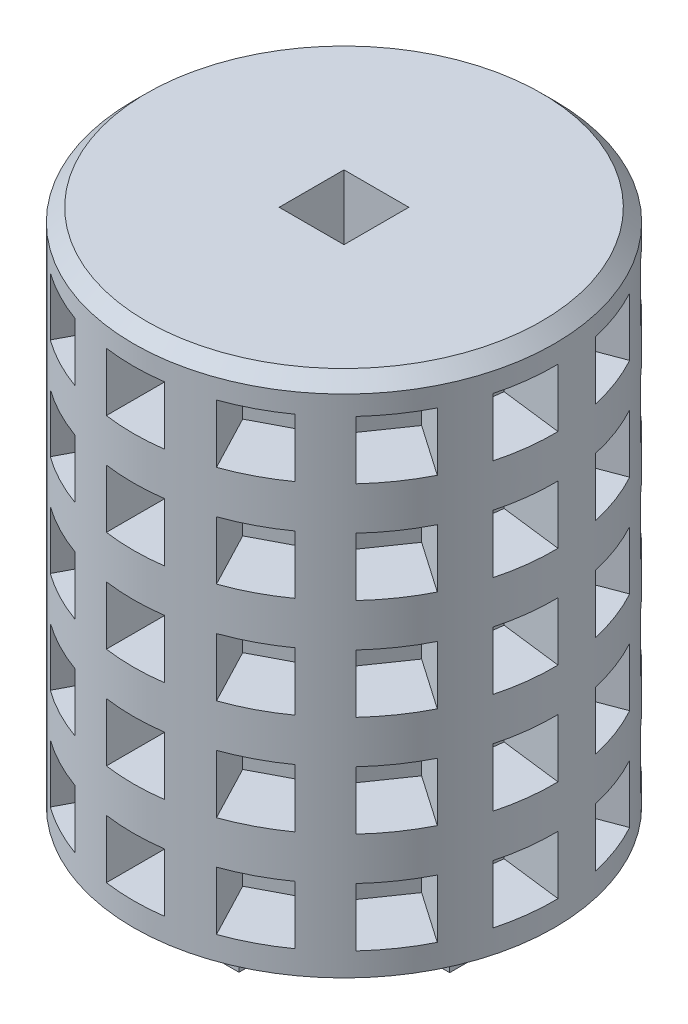
SolidWorks part; units mm, degrees
ref_plane "Front Plane" through (0, 0, 0) normal (0, 0, 1) x (1, 0, 0)
ref_plane "Top Plane" through (0, 0, 0) normal (0, 1, 0) x (1, 0, 0)
ref_plane "Right Plane" through (0, 0, 0) normal (1, 0, 0) x (0, 0, -1)
sketch "Sketch1" plane through (0, 0, 0) normal (0, 1, 0) x (1, 0, 0)
  circle A0 centre (0, 0) radius 41.2369
  dimension "D1" = 82.4738
extrude "Boss-Extrude1" add sketch "Sketch1" along normal blind 203.2 contours A0
sketch "Sketch2" plane through (0, 0, 0) normal (0, -1, 0) x (-1, 0, 0)
  line L3 (0, -6.35) -> (6.35, -6.35)
  line L5 (0, 6.35) -> (6.35, 6.35)
  line L6 (6.35, -6.35) -> (6.35, 6.35)
  line L7 (0, -6.35) -> (-6.35, -6.35)
  line L9 (0, 6.35) -> (-6.35, 6.35)
  line L10 (-6.35, -6.35) -> (-6.35, 6.35)
extrude "Cut-Extrude1" cut sketch "Sketch2" against normal through all contours L10 L9 L5 L6 L3 L7
ref_plane "Plane2" through (0, 0, 60.96) normal (0, 0, 1) x (1, 0, 0)
chamfer "Chamfer1" distance 2.54 angle 45 1 edges at (0, 203.2, 41.2369)
chamfer "Chamfer2" distance 2.54 angle 45 1 edges at (0, 0, 41.2369)
ref_plane "Plane3" through (0, 0, 48.26) normal (0, 0, 1) x (1, 0, 0)
ref_plane "Plane4" through (0, 0, 41.402) normal (0, 0, 1) x (1, 0, 0)
sketch "Sketch3" plane through (0, 0, 41.402) normal (0, 0, 1) x (1, 0, 0)
  line L0 (-41.2369, 200.66) -> (41.2369, 200.66) construction
  line L1 (0, 200.66) -> (-9.525, 200.66)
  line L2 (-9.525, 200.66) -> (9.525, 181.61)
  line L3 (-3.81, 181.61) -> (-9.525, 181.61)
  line L4 (-9.525, 200.66) -> (-9.525, 181.61)
  line L5 (-9.525, 181.61) -> (9.525, 200.66)
  line L6 (0, 200.66) -> (9.525, 200.66)
  line L8 (-3.81, 181.61) -> (9.525, 181.61)
  line L9 (9.525, 200.66) -> (9.525, 181.61)
sketch "Sketch6" plane through (0, 0, 41.402) normal (0, 0, 1) x (1, 0, 0)
  line L0 (-9.525, 181.61) -> (9.525, 200.66) construction
  line L3 (0, 196.85) -> (5.715, 196.85)
  line L4 (5.715, 191.135) -> (5.715, 196.85)
  line L5 (-9.525, 200.66) -> (9.525, 181.61) construction
  line L8 (0, 196.85) -> (-5.715, 196.85)
  line L9 (-5.715, 191.135) -> (-5.715, 196.85)
  line L12 (-5.715, 191.135) -> (-5.715, 185.42)
  line L13 (-5.715, 185.42) -> (5.715, 185.42)
  line L14 (5.715, 191.135) -> (5.715, 185.42)
extrude "Cut-Extrude3" cut sketch "Sketch6" against normal blind 12.7 contours L3 L4 L14 L13 L12 L9 L8
pattern_linear "LPattern1" count 10 spacing 19.812 along (0, -1, 0) of "Cut-Extrude3"
pattern_circular "CirPattern1" count 13 every 27.7 about axis through (0, 0, 0) along (0, 1, 0) of "LPattern1", "Cut-Extrude3"
sketch "Sketch7" plane through (0, 0, 0) normal (0, -1, 0) x (1, 0, 0)
  circle A0 centre (0, 0) radius 41.2369
extrude "Cut-Extrude4" cut sketch "Sketch7" against normal blind 101.6 contours A0
sketch "Sketch9" plane through (0, 101.6, 0) normal (0, -1, 0) x (1, 0, 0)
  line L3 (-6.35, -6.35) -> (-6.35, 6.35) construction
  line L4 (-26.543, -5.969) -> (-24.257, -5.969)
  line L5 (-26.543, -5.969) -> (-26.543, 5.969)
  line L6 (-26.543, 5.969) -> (-24.257, 5.969)
  line L7 (-24.257, -5.969) -> (-24.257, 5.969)
  line L8 (-26.543, -5.969) -> (-24.257, 5.969) construction
  line L9 (-26.543, 5.969) -> (-24.257, -5.969) construction
  line L10 (-5.969, 24.257) -> (5.969, 24.257)
  line L11 (-5.969, 24.257) -> (-5.969, 26.543)
  line L12 (-5.969, 26.543) -> (5.969, 26.543)
  line L13 (5.969, 24.257) -> (5.969, 26.543)
  line L14 (-5.969, 24.257) -> (5.969, 26.543) construction
  line L15 (-5.969, 26.543) -> (5.969, 24.257) construction
  line L16 (26.67, -5.969) -> (24.13, -5.969)
  line L17 (26.67, -5.969) -> (26.67, 5.969)
  line L18 (26.67, 5.969) -> (24.13, 5.969)
  line L19 (24.13, -5.969) -> (24.13, 5.969)
  line L20 (26.67, -5.969) -> (24.13, 5.969) construction
  line L21 (26.67, 5.969) -> (24.13, -5.969) construction
  line L22 (-5.969, -26.543) -> (5.969, -26.543)
  line L23 (-5.969, -26.543) -> (-5.969, -24.257)
  line L24 (-5.969, -24.257) -> (5.969, -24.257)
  line L25 (5.969, -26.543) -> (5.969, -24.257)
  line L26 (-5.969, -26.543) -> (5.969, -24.257) construction
  line L27 (-5.969, -24.257) -> (5.969, -26.543) construction
  line L28 (-6.35, 6.35) -> (6.35, 6.35) construction
  line L29 (6.35, -6.35) -> (6.35, 6.35) construction
  line L30 (-6.35, -6.35) -> (6.35, -6.35) construction
  point P5 (-25.4, 0)
  point P12 (0, 25.4)
  point P17 (25.4, 0)
  point P22 (0, -25.4)
  dimension "D1" = 19.05
  dimension "D2" = 19.05
  dimension "D3" = 19.05
  dimension "D4" = 19.05
  dimension "D5" = 2.286
  dimension "D6" = 11.938
  dimension "D7" = 2.286
  dimension "D8" = 11.938
  dimension "D9" = 11.938
  dimension "D10" = 2.286
  dimension "D11" = 2.54
  dimension "D12" = 11.938
extrude "Boss-Extrude2" add sketch "Sketch9" along normal blind 11.938
